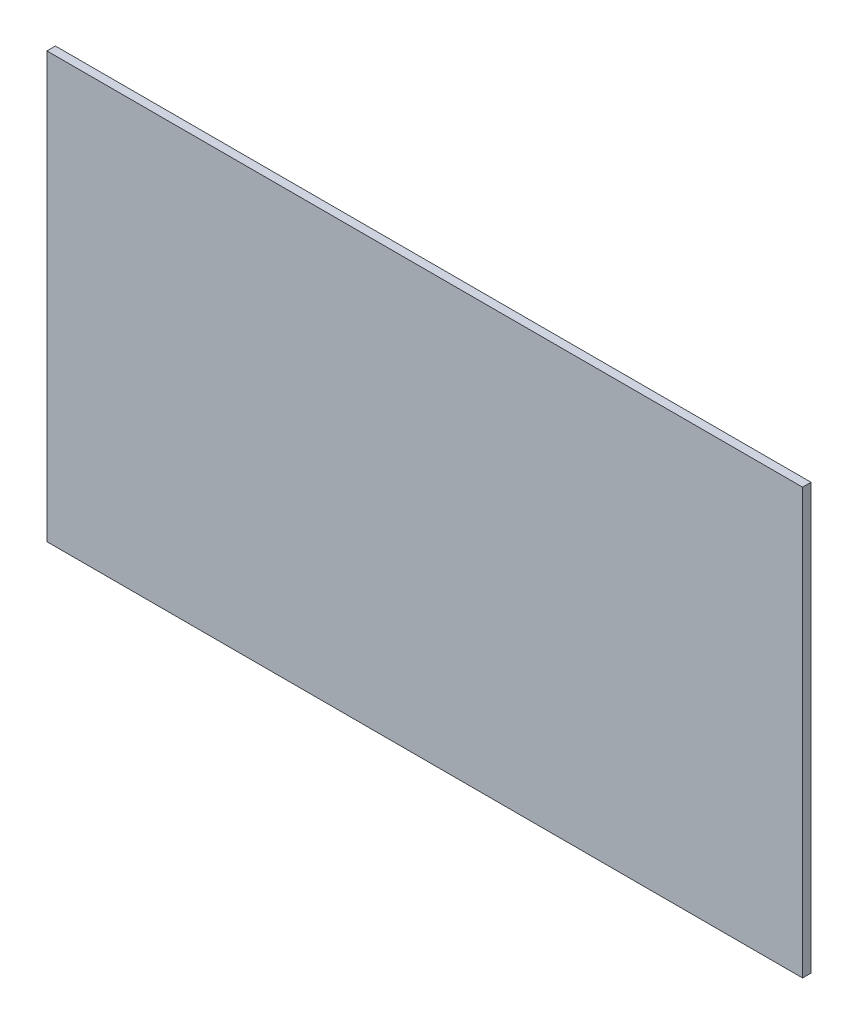
SolidWorks part; units mm, degrees
material "Pine"
ref_plane "Front Plane" through (0, 0, 0) normal (0, 0, 1) x (1, 0, 0)
ref_plane "Top Plane" through (0, 0, 0) normal (0, 1, 0) x (1, 0, 0)
ref_plane "Right Plane" through (0, 0, 0) normal (1, 0, 0) x (0, 0, -1)
sketch "Sketch1" plane through (0, 0, 0) normal (0, 0, 1) x (1, 0, 0)
  line L1 (-672.3948, 478.8289) -> (953.2052, 478.8289)
  line L2 (-672.3948, 478.8289) -> (-672.3948, -435.5711)
  line L3 (-672.3948, -435.5711) -> (953.2052, -435.5711)
  line L4 (953.2052, 478.8289) -> (953.2052, -435.5711)
  dimension "D1" = 1625.6
  dimension "D2" = 914.4
extrude "Boss-Extrude1" add sketch "Sketch1" along normal blind 18.2562
